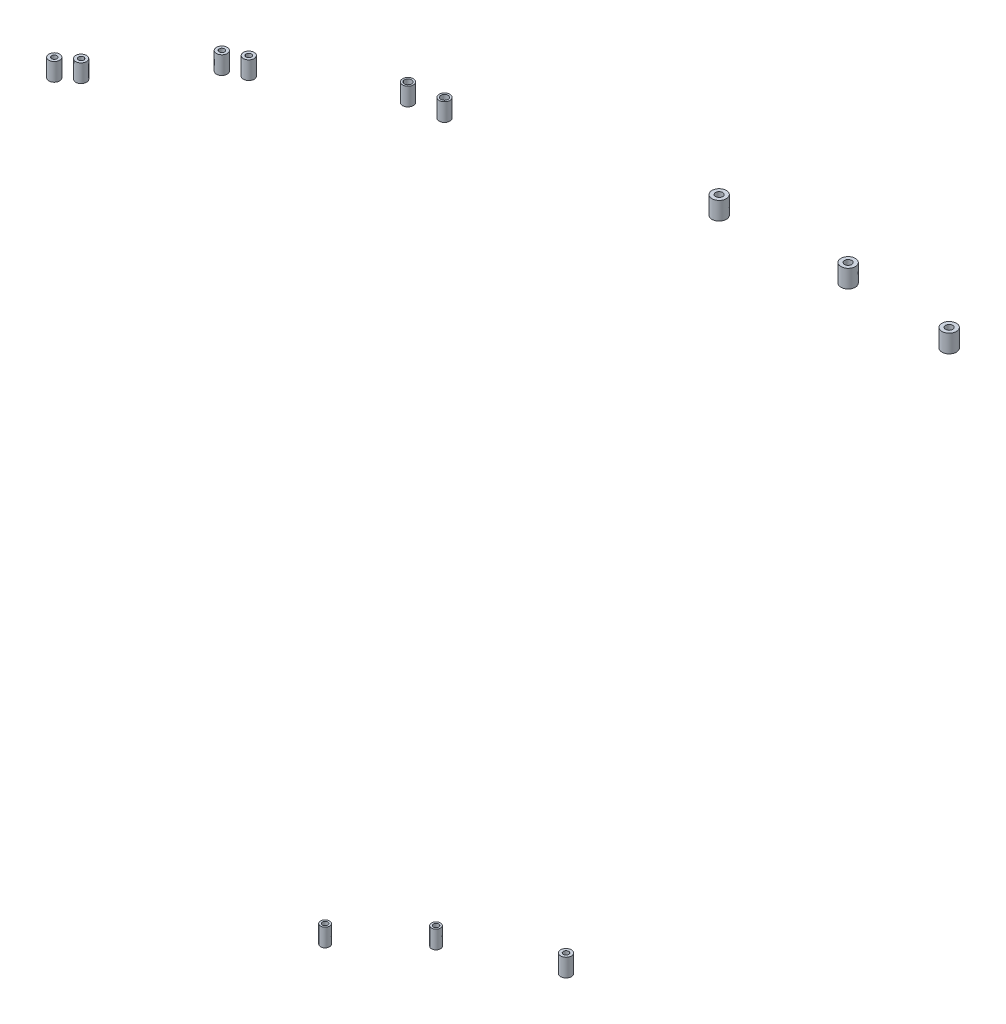
SolidWorks part; units mm, degrees
material "7075-O (SS)"
ref_plane "Płaszczyzna XY" through (0, 0, 0) normal (0, 0, 1) x (1, 0, 0)
ref_plane "Płaszczyzna XZ" through (0, 0, 0) normal (0, 1, 0) x (1, 0, 0)
ref_plane "Płaszczyzna YZ" through (0, 0, 0) normal (1, 0, 0) x (0, 0, -1)
sketch "Szkic1" plane through (0, 700, 0) normal (0, 1, 0) x (1, 0, 0)
  circle A0 centre (-474.4468, -382.6878) radius 3 construction
  circle A1 centre (-466.3081, -375.8594) radius 3 construction
  circle A2 centre (-431.0397, -332.7742) radius 3 construction
  circle A3 centre (-421.0901, -327.7251) radius 3 construction
  circle A4 centre (-364.0511, -296.1018) radius 3 construction
  circle A5 centre (-346.3899, -293.3962) radius 3 construction
  circle A6 centre (-223.0248, -263.8022) radius 4 construction
  circle A7 centre (-154.3447, -260.6438) radius 4 construction
  circle A8 centre (-94.9095, -263.8022) radius 4 construction
  circle A9 centre (-474.4468, -382.6878) radius 3
  circle A10 centre (-466.3081, -375.8594) radius 3
  circle A11 centre (-431.0397, -332.7742) radius 3
  circle A12 centre (-421.0901, -327.7251) radius 3
  circle A13 centre (-364.0511, -296.1018) radius 3
  circle A14 centre (-346.3899, -293.3962) radius 3
  circle A15 centre (-223.0248, -263.8022) radius 4
  circle A16 centre (-154.3447, -260.6438) radius 4
  circle A17 centre (-94.9095, -263.8022) radius 4
  circle A18 centre (-94.9095, -263.8022) radius 2
  circle A19 centre (-154.3447, -260.6438) radius 2
  circle A20 centre (-223.0248, -263.8022) radius 2
  circle A21 centre (-346.3899, -293.3962) radius 2
  circle A22 centre (-364.0511, -296.1018) radius 2
  circle A23 centre (-421.0901, -327.7251) radius 1.5
  circle A24 centre (-431.0397, -332.7742) radius 1.5
  circle A25 centre (-466.3081, -375.8594) radius 1.5
  circle A26 centre (-474.4468, -382.6878) radius 1.5
  dimension "D1" = 4
  dimension "D2" = 4
  dimension "D3" = 4
  dimension "D4" = 4
  dimension "D5" = 4
  dimension "D6" = 3
  dimension "D7" = 3
  dimension "D8" = 3
  dimension "D9" = 3
extrude "Dodanie-wyciągnięcie1" add sketch "Szkic1" against normal blind 10
sketch "Szkic2" plane through (0, 310.2, 0) normal (0, 1, 0) x (1, 0, 0)
  circle A0 centre (-370.9569, -335.3671) radius 2.5 construction
  circle A1 centre (-339.083, -305.4298) radius 2.5 construction
  circle A2 centre (-289.6871, -282.4241) radius 3 construction
  circle A3 centre (-370.9569, -335.3671) radius 2.5
  circle A4 centre (-339.083, -305.4298) radius 2.5
  circle A5 centre (-289.6871, -282.4241) radius 3
  circle A6 centre (-289.6871, -282.4241) radius 1.5
  circle A7 centre (-339.083, -305.4298) radius 1.5
  circle A8 centre (-370.9569, -335.3671) radius 1.5
  dimension "D1" = 3
  dimension "D2" = 3
  dimension "D3" = 3
extrude "Dodanie-wyciągnięcie2" add sketch "Szkic2" against normal blind 10 separate body
